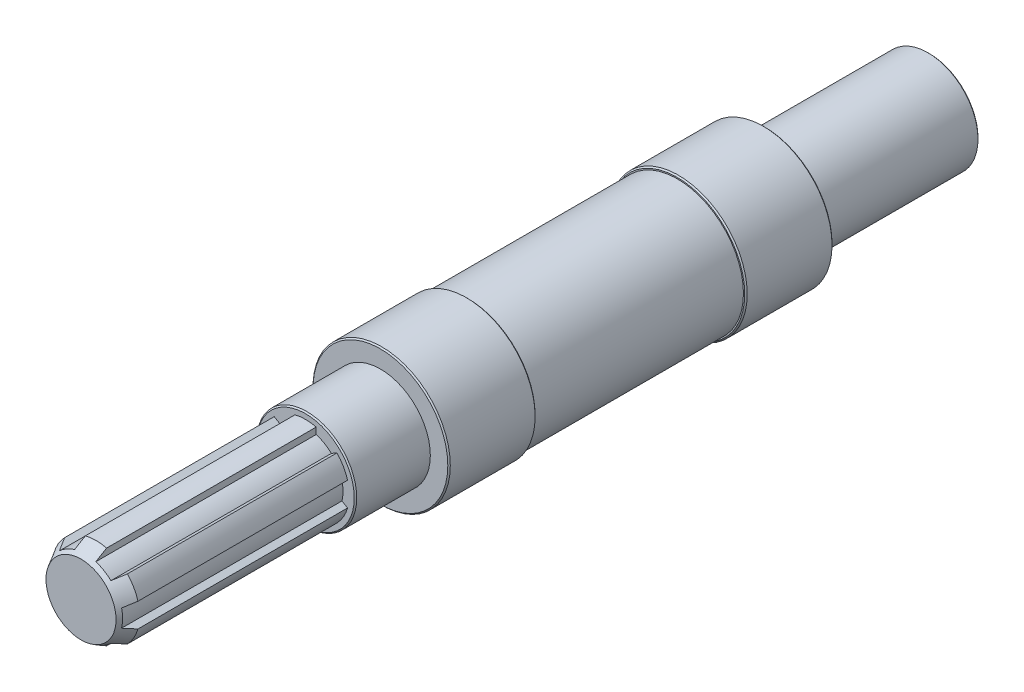
SolidWorks part; units mm, degrees
ref_plane "Přední rovina" through (0, 0, 0) normal (0, 0, 1) x (1, 0, 0)
ref_plane "Horní rovina" through (0, 0, 0) normal (0, 1, 0) x (1, 0, 0)
ref_plane "Pravá rovina" through (0, 0, 0) normal (1, 0, 0) x (0, 0, -1)
sketch "Skica1" plane through (0, 0, 0) normal (0, 0, 1) x (1, 0, 0)
  circle A0 centre (0, 0) radius 20
  dimension "D1" = 40
extrude "Přidat vysunutím1" add sketch "Skica1" along normal blind 66
sketch "Skica2" plane through (0, 0, 66) normal (0, 0, 1) x (1, 0, 0)
  circle A0 centre (0, 0) radius 27.5
  dimension "D1" = 55
extrude "Přidat vysunutím2" add sketch "Skica2" along normal blind 35
sketch "Skica3" plane through (0, 0, 101) normal (0, 0, 1) x (1, 0, 0)
  circle A0 centre (0, 0) radius 26.5
  dimension "D1" = 53
extrude "Přidat vysunutím3" add sketch "Skica3" along normal blind 84
sketch "Skica4" plane through (0, 0, 185) normal (0, 0, 1) x (1, 0, 0)
  circle A0 centre (0, 0) radius 27.5
  dimension "D1" = 55
extrude "Přidat vysunutím4" add sketch "Skica4" along normal blind 35
sketch "Skica5" plane through (0, 0, 220) normal (0, 0, 1) x (1, 0, 0)
  circle A0 centre (0, 0) radius 20
  dimension "D1" = 40
extrude "Přidat vysunutím5" add sketch "Skica5" along normal blind 30
sketch "Skica6" plane through (0, 0, 250) normal (0, 0, 1) x (1, 0, 0)
  circle A0 centre (0, 0) radius 17.5
  dimension "D1" = 35
extrude "Přidat vysunutím6" add sketch "Skica6" along normal blind 90
chamfer "Zkosení3" distance 6 angle 30 1 edges at (17.5, 0, 340)
sketch "Skica9" plane through (0, 0, 340) normal (0, 0, 1) x (1, 0, 0)
  line L0 (0, 17.5) -> (0, -17.5) construction
  line L1 (-4.25, 14.3853) -> (-4.25, 16.9761)
  line L2 (4.25, 14.3853) -> (4.25, 16.9761)
  line L3 (10.3331, 10.8733) -> (12.5767, 12.1687)
  line L4 (14.5831, 3.5121) -> (16.8267, 4.8074)
  line L5 (14.5831, -3.5121) -> (16.8267, -4.8074)
  line L6 (10.3331, -10.8733) -> (12.5767, -12.1687)
  line L7 (4.25, -14.3853) -> (4.25, -16.9761)
  line L8 (-4.25, -14.3853) -> (-4.25, -16.9761)
  line L9 (-10.3331, -10.8733) -> (-12.5767, -12.1687)
  line L10 (-14.5831, -3.5121) -> (-16.8267, -4.8074)
  line L11 (-14.5831, 3.5121) -> (-16.8267, 4.8074)
  line L12 (-10.3331, 10.8733) -> (-12.5767, 12.1687)
  arc A0 (-14.5831, 3.5121) -> (-14.5831, -3.5121) centre (0, 0) ccw
  circle A1 centre (0, 0) radius 17.5 construction
  arc A3 (-12.5767, 12.1687) -> (-16.8267, 4.8074) centre (0, 0) ccw
  arc A8 (-4.25, 14.3853) -> (-10.3331, 10.8733) centre (0, 0) ccw
  arc A9 (-10.3331, -10.8733) -> (-4.25, -14.3853) centre (0, 0) ccw
  arc A10 (4.25, -14.3853) -> (10.3331, -10.8733) centre (0, 0) ccw
  arc A11 (14.5831, -3.5121) -> (14.5831, 3.5121) centre (0, 0) ccw
  arc A12 (10.3331, 10.8733) -> (4.25, 14.3853) centre (0, 0) ccw
  arc A13 (4.25, 16.9761) -> (-4.25, 16.9761) centre (0, 0) ccw
  arc A19 (16.8267, 4.8074) -> (12.5767, 12.1687) centre (0, 0) ccw
  arc A25 (12.5767, -12.1687) -> (16.8267, -4.8074) centre (0, 0) ccw
  arc A31 (-4.25, -16.9761) -> (4.25, -16.9761) centre (0, 0) ccw
  arc A37 (-16.8267, -4.8074) -> (-12.5767, -12.1687) centre (0, 0) ccw
  point P41 (0, 0)
  dimension "D1" = 30
  dimension "D2" = 6
  dimension "D3" = 8.5
extrude "Odebrat vysunutím16" cut sketch "Skica9" against normal blind 90 flip side to cut
chamfer "Zkosení4" distance 0.5 angle 45 6 edges at (20, 0, 0) (27.5, 0, 66) (27.5, 0, 101) (27.5, 0, 185) (27.5, 0, 220) (20, 0, 250)
hole_wizard "M10 závit1" positions "Skica11" profile "Skica10" tap size "M10" standard "ISO"
sketch "Skica11" plane through (0, 0, 0) normal (0, 0, -1) x (-1, 0, 0)
  point P0 (0, 0)
sketch "Skica10" plane through (0, 0, 0) normal (1, 0, 0) x (0, 1, 0)
  line L0 (0, 0) -> (0, 32.5537)
  line L1 (0, 32.5537) -> (4.25, 30)
  line L2 (4.25, 30) -> (4.25, 0)
  line L5 (4.25, 0) -> (0, 0)
  line L10 (0, 32.5537) -> (-4.25, 30) construction
  line L11 (0, -6.35) -> (0, 107.95) construction
  dimension "Průměr závitníku" = 8.5
  dimension "Hloubka závitníku" = 30
  dimension "Úhel vrtání" = 118
cosmetic thread "Závit díry1" parameters "D1"=30, "D2"=10
sketch "Skica12" plane through (0, 0, 0) normal (0, 1, 0) x (1, 0, 0)
  line L0 (0, 0) -> (0, -66) construction
  line L1 (27, -66) -> (-27, -66) construction
  line L2 (-7, 0) -> (-7, -59)
  line L3 (7, 0) -> (-7, 0)
  line L4 (19.5, 0) -> (-19.5, 0) construction
  line L5 (7, 0) -> (7, -59)
  line L6 (20, -66) -> (-20, -66) construction
  arc A0 (-7, -59) -> (7, -59) centre (0, -59) ccw
  point P3 (0, -31.697)
  dimension "D3" = 14
  dimension "D4" = 7
  dimension "D2" = 7
